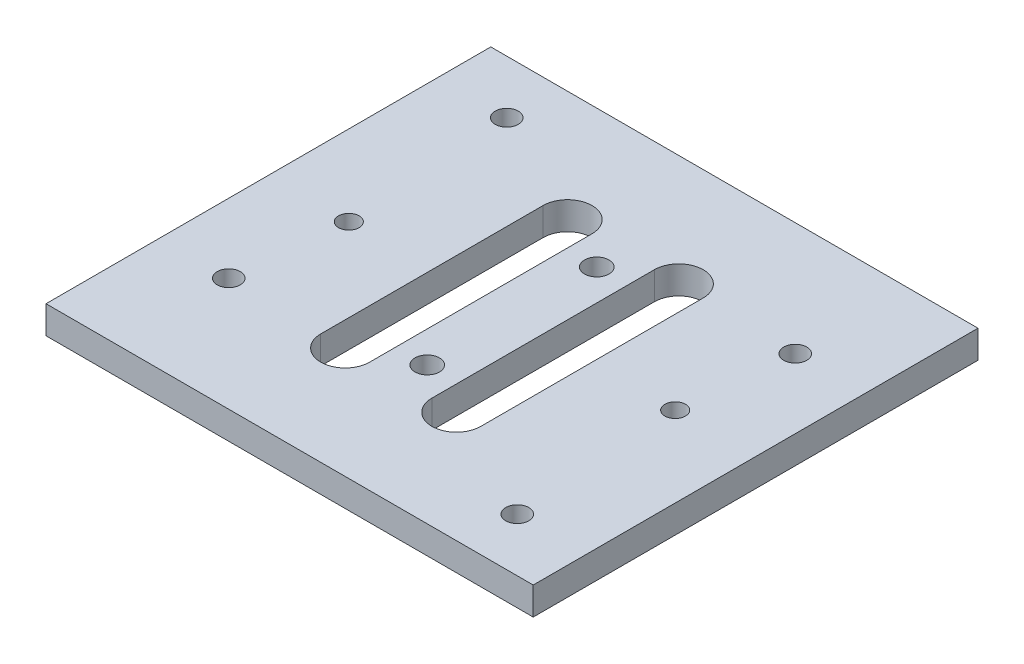
SolidWorks part; units mm, degrees
ref_plane "Front Plane" through (0, 0, 0) normal (0, 0, 1) x (1, 0, 0)
ref_plane "Top Plane" through (0, 0, 0) normal (0, 1, 0) x (1, 0, 0)
ref_plane "Right Plane" through (0, 0, 0) normal (1, 0, 0) x (0, 0, -1)
sketch "Sketch1" plane through (0, 0, 0) normal (0, 1, 0) x (1, 0, 0)
  line L1 (0, 0) -> (87.63, 0)
  line L2 (0, 0) -> (0, 80)
  line L3 (0, 80) -> (87.63, 80)
  line L4 (87.63, 0) -> (87.63, 80)
  dimension "D1" = 87.63
  dimension "D2" = 80
extrude "Boss-Extrude1" add sketch "Sketch1" along normal blind 5
sketch "Sketch2" plane through (0, 5, 0) normal (0, 1, 0) x (1, 0, 0)
  line L0 (0, 80) -> (0, 0) construction
  line L1 (87.63, 80) -> (0, 80) construction
  circle A0 centre (12.465, 70.4) radius 2.075
  circle A1 centre (12.465, 20.4) radius 2.075
  circle A2 centre (14.465, 40) radius 1.85
  circle A3 centre (73.165, 40) radius 1.85
  circle A4 centre (75.165, 9.6) radius 2.075
  circle A5 centre (75.165, 59.6) radius 2.075
  dimension "D1" = 4.15
  dimension "D3" = 9.6
  dimension "D4" = 4.15
  dimension "D5" = 60.8
  dimension "D6" = 62.7
  dimension "D7" = 4.15
  dimension "D8" = 4.15
  dimension "D9" = 62.7
  dimension "D10" = 10.8
  dimension "D11" = 3.7
  dimension "D12" = 3.7
  dimension "D13" = 60.7
  dimension "D14" = 30.4
  dimension "D15" = 50
  dimension "D16" = 2
  dimension "D17" = 30.4
  dimension "D2" = 12.465
extrude "Cut-Extrude1" cut sketch "Sketch2" against normal through all
sketch "Sketch3" plane through (0, 5, 0) normal (0, 1, 0) x (1, 0, 0)
  line L5 (87.63, 80) -> (0, 80) construction
  line L6 (0, 0) -> (87.63, 0) construction
  line L7 (0, 80) -> (0, 0) construction
  line L8 (87.63, 0) -> (87.63, 80) construction
  circle A0 centre (43.81, 55.25) radius 2.2
  circle A1 centre (43.82, 24.75) radius 2.2
  dimension "D1" = 4.4
  dimension "D2" = 4.4
  dimension "D4" = 24.75
  dimension "D6" = 43.82
  dimension "D3" = 24.75
  dimension "D5" = 43.82
extrude "Cut-Extrude2" cut sketch "Sketch3" against normal up to next
sketch "Sketch4" plane through (0, 5, 0) normal (0, 1, 0) x (1, 0, 0)
  line L0 (33.81, 60) -> (33.81, 20) construction
  line L1 (38.21, 60) -> (38.21, 20)
  line L2 (29.41, 60) -> (29.41, 20)
  line L5 (53.81, 60) -> (53.81, 20) construction
  line L6 (58.21, 60) -> (58.21, 20)
  line L7 (49.41, 60) -> (49.41, 20)
  line L10 (0, 0) -> (87.63, 0) construction
  line L11 (87.63, 80) -> (0, 80) construction
  arc A0 (38.21, 60) -> (29.41, 60) centre (33.81, 60) ccw
  arc A1 (29.41, 20) -> (38.21, 20) centre (33.81, 20) ccw
  circle A3 centre (43.81, 55.25) radius 2.2 construction
  arc A6 (58.21, 60) -> (49.41, 60) centre (53.81, 60) ccw
  arc A7 (49.41, 20) -> (58.21, 20) centre (53.81, 20) ccw
  point P2 (33.81, 40)
  point P15 (53.81, 40)
  dimension "D1" = 10
  dimension "D2" = 20
  dimension "D3" = 2
  dimension "D4" = 20
extrude "Cut-Extrude3" cut sketch "Sketch4" against normal up to next
